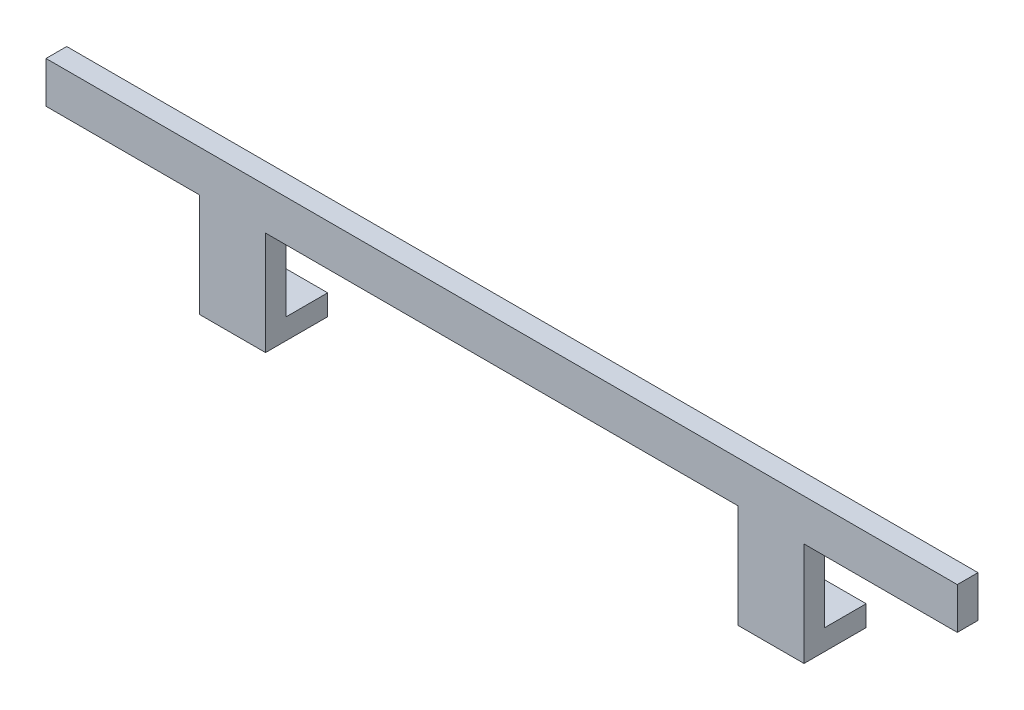
SolidWorks part; units mm, degrees
ref_plane "Alzado" through (0, 0, 0) normal (0, 0, 1) x (1, 0, 0)
ref_plane "Planta" through (0, 0, 0) normal (0, 1, 0) x (1, 0, 0)
ref_plane "Vista lateral" through (0, 0, 0) normal (1, 0, 0) x (0, 0, -1)
sketch "Croquis1" plane through (0, 0, 0) normal (0, 0, 1) x (1, 0, 0)
  line L0 (0, 0) -> (0, 30) construction
  line L1 (-110, 30) -> (110, 30) construction
  line L2 (-110, 25) -> (-73, 25)
  line L3 (-110, 35) -> (110, 35)
  line L4 (-110, 35) -> (-110, 25)
  line L5 (110, 35) -> (110, 25)
  line L6 (65, 0) -> (65, 30) construction
  line L7 (-65, 0) -> (-65, 30) construction
  line L8 (-57, 0) -> (-57, 25)
  line L9 (73, 0) -> (73, 25)
  line L10 (-73, 0) -> (-73, 25)
  line L11 (57, 0) -> (57, 25)
  line L12 (-57, 25) -> (57, 25)
  line L13 (-73, 0) -> (-73, 30) construction
  line L14 (-57, 0) -> (-57, 30) construction
  line L15 (73, 25) -> (110, 25)
  line L16 (-110, 25) -> (110, 25) construction
  line L17 (57, 0) -> (57, 30) construction
  line L18 (-73, 0) -> (-57, 0)
  line L19 (73, 0) -> (73, 30) construction
  line L20 (57, 0) -> (73, 0)
  point P10 (0, 30)
  dimension "D1" = 30
  dimension "D4" = 220
  dimension "D2" = 5
  dimension "D3" = 5
  dimension "D5" = 65
  dimension "D6" = 65
  dimension "D7" = 8
  dimension "D8" = 8
extrude "Saliente-Extruir1" add sketch "Croquis1" along normal blind 5
sketch "Croquis2" plane through (0, 0, 0) normal (0, 0, -1) x (-1, 0, 0)
  line L12 (73, 0) -> (73, 5)
  line L13 (-57, 5) -> (-73, 5)
  line L14 (73, 5) -> (57, 5)
  line L16 (-73, 0) -> (-57, 0)
  line L17 (-73, 0) -> (-73, 5)
  line L18 (-57, 0) -> (-57, 5)
  line L20 (57, 0) -> (57, 5)
  line L22 (57, 0) -> (73, 0)
  line L23 (-57, 5) -> (-73, 5)
  dimension "D1" = 5
extrude "Saliente-Extruir2" add sketch "Croquis2" along normal blind 10
sketch "Croquis3" plane through (0, 5, 0) normal (0, 1, 0) x (1, 0, 0)
  line L0 (65, 10) -> (65, 0) construction
  line L1 (57, 10) -> (73, 10) construction
  line L2 (57, 0) -> (73, 0) construction
  line L3 (-65, 10) -> (-65, 0) construction
  line L4 (-73, 10) -> (-57, 10) construction
  line L5 (-73, 0) -> (-57, 0) construction
  circle A0 centre (65, 5) radius 2
  circle A1 centre (-65, 5) radius 2
extrude "Cortar-Extruir1" cut sketch "Croquis3" against normal up to next
